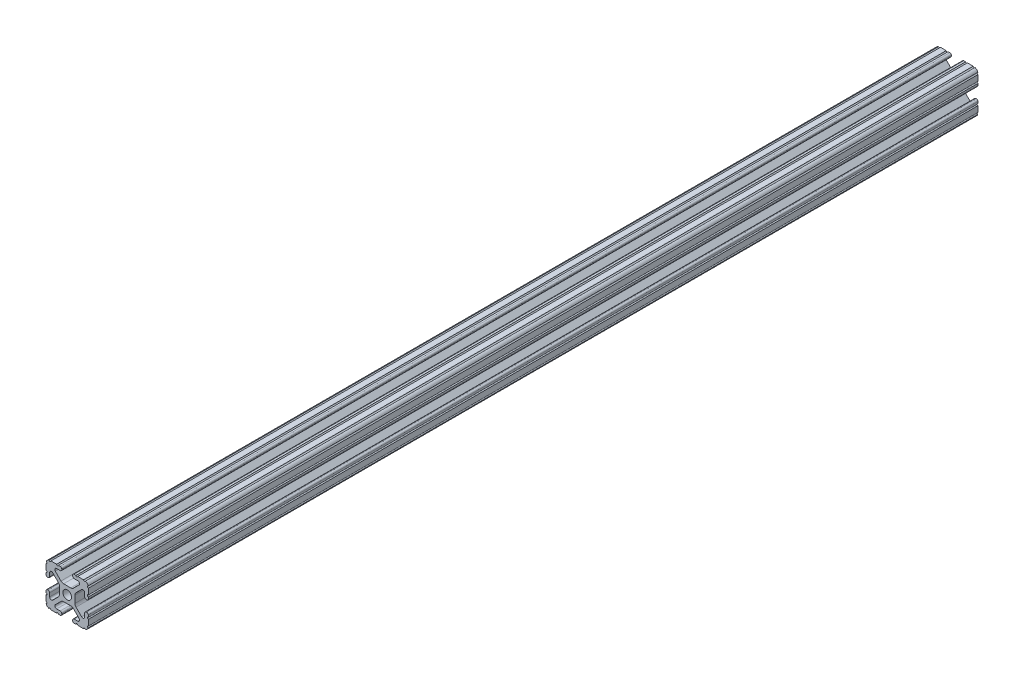
SolidWorks part; units mm, degrees
ref_plane "Front Plane" through (0, 0, 0) normal (0, 0, 1) x (1, 0, 0)
ref_plane "Top Plane" through (0, 0, 0) normal (0, 1, 0) x (1, 0, 0)
ref_plane "Right Plane" through (0, 0, 0) normal (1, 0, 0) x (0, 0, -1)
sketch "Sketch2" plane through (0, 0, 0) normal (0, 0, 1) x (1, 0, 0)
  line L0 (0, 12.7) -> (0, -12.7) construction
  line L1 (-12.7, 0) -> (12.7, 0) construction
  line L2 (3.2512, -12.7) -> (12.7, -12.7)
  line L3 (12.7, -12.7) -> (12.7, -3.2512)
  line L4 (3.2512, -12.7) -> (3.2512, -10.4902)
  line L5 (3.2512, -10.4902) -> (8.9276, -10.4902)
  line L6 (8.9276, -10.4902) -> (3.0856, -4.6482)
  line L7 (0, 0) -> (12.7, -12.7) construction
  line L8 (12.7, -3.2512) -> (10.4902, -3.2512)
  line L9 (10.4902, -3.2512) -> (10.4902, -8.9276)
  line L10 (10.4902, -8.9276) -> (4.6482, -3.0856)
  circle A0 centre (0, 0) radius 2.6035
  arc A1 (6.3485, -10.4902) -> (7.1039, -8.6665) centre (6.3485, -9.4219) ccw construction
  point P8 (0, -4.6482)
  dimension "Center Hole Diameter" = 5.207
  dimension "Rail Height" = 25.4
  dimension "Rail Width" = 25.4
  dimension "T-Slot Width" = 6.5024
  dimension "Slot Inner Width" = 14.8336
  dimension "Thickness" = 2.2098
  dimension "Slot Depth" = 5.842
  dimension "D1" = 2.2098
sketch "Sketch3" plane through (0, 0, 0) normal (1, 0, 0) x (0, 0, -1)
  line L0 (-228.6, -12.7) -> (228.6, -12.7) construction
  line L1 (-205.74, 0) -> (205.74, 0) construction
  dimension "Length" = 457.2
  dimension "D1" = 411.48
sketch "Sketch4" plane through (0, 0, 0) normal (0, 0, 1) x (1, 0, 0)
  line L0 (4.1904, -12.7) -> (10.1173, -12.7)
  line L1 (3.2512, -12.7) -> (12.7, -12.7) construction
  line L2 (3.2512, -12.7) -> (3.2512, -10.4902) construction
  line L3 (3.2512, -10.4902) -> (8.9276, -10.4902) construction
  line L4 (3.2512, -11.4294) -> (3.2512, -11.7608)
  line L5 (4.1904, -10.4902) -> (6.3485, -10.4902)
  line L6 (0, -4.6482) -> (2.164, -4.6482)
  line L7 (8.9276, -10.4902) -> (3.0856, -4.6482) construction
  line L8 (3.7373, -5.2999) -> (7.1039, -8.6665)
  line L9 (12.7, -12.7) -> (12.7, -3.2512) construction
  line L10 (10.4902, -8.9276) -> (4.6482, -3.0856) construction
  line L11 (10.4902, -3.2512) -> (10.4902, -8.9276) construction
  line L12 (10.4902, -6.3485) -> (10.4902, -4.1904)
  line L13 (12.7, -3.2512) -> (10.4902, -3.2512) construction
  line L14 (11.4294, -3.2512) -> (11.7608, -3.2512)
  line L15 (12.7, -4.1904) -> (12.7, -10.1173)
  line L16 (8.6665, -7.1039) -> (5.2999, -3.7373)
  line L17 (4.6482, 0) -> (4.6482, -2.164)
  line L18 (-12.7, 0) -> (12.7, 0) construction
  line L19 (0, -4.6482) -> (0, -2.6035)
  line L20 (0, 12.7) -> (0, -12.7) construction
  line L21 (4.6482, 0) -> (2.6035, 0)
  arc A0 (3.2512, -11.7608) -> (4.1904, -12.7) centre (4.1904, -11.7608) ccw
  arc A2 (3.2512, -11.4294) -> (4.1904, -10.4902) centre (4.1904, -11.4294) cw
  arc A3 (6.3485, -10.4902) -> (7.1039, -8.6665) centre (6.3485, -9.4219) ccw
  arc A4 (2.164, -4.6482) -> (3.7373, -5.2999) centre (2.164, -6.8732) cw
  arc A5 (10.1173, -12.7) -> (12.7, -10.1173) centre (10.1173, -10.1173) ccw
  arc A6 (8.6665, -7.1039) -> (10.4902, -6.3485) centre (9.4219, -6.3485) ccw
  arc A7 (10.4902, -4.1904) -> (11.4294, -3.2512) centre (11.4294, -4.1904) cw
  arc A8 (11.7608, -3.2512) -> (12.7, -4.1904) centre (11.7608, -4.1904) cw
  arc A9 (5.2999, -3.7373) -> (4.6482, -2.164) centre (6.8732, -2.164) cw
  circle A10 centre (0, 0) radius 2.6035 construction
  arc A11 (0, -2.6035) -> (2.6035, 0) centre (0, 0) ccw
  dimension "D1" = 2.5827
  dimension "D2" = 2.225
  dimension "D3" = 0.9392
extrude "Boss-Extrude1" add sketch "Sketch4" along normal mid plane 533.2
sketch "Sketch5" plane through (0, 0, 0) normal (0, 0, 1) x (1, 0, 0)
  line L0 (3.2512, -12.7) -> (12.7, -12.7) construction
  line L1 (4.1904, -10.4902) -> (6.3485, -10.4902) construction
  line L3 (0, 0) -> (12.7, -12.7) construction
  line L4 (6.3485, -10.4902) -> (6.3485, -12.7) construction
  line L5 (8.9276, -10.4902) -> (3.0856, -4.6482) construction
  circle A0 centre (10.3562, -12.7) radius 0.5524
  circle A1 centre (5.796, -12.7) radius 0.5524
  circle A2 centre (12.7, -10.3562) radius 0.5524
  circle A3 centre (12.7, -5.796) radius 0.5524
  point P10 (5.2694, -10.4902)
  point P12 (9.4219, -6.3485)
  dimension "D1" = 1.1049
extrude "Cut-Extrude1" cut sketch "Sketch5" against normal through all both and the other way through all
mirror "Mirror1" about plane through (0, 0, 0) normal (1, 0, 0) of bodies 137 134
mirror "Mirror2" about plane through (0, 0, 0) normal (0, 1, 0) of bodies 135
equation "\"D1@Boss-Extrude1\"=\"Length@Sketch3\""
equation "\"D1@Sketch2\"=\"Thickness@Sketch2\""
equation "\"D2@Sketch4\"=\"Slot Inner Width@Sketch2\"*0.15"
equation "\"D1@Sketch4\"=\"D3@Sketch4\"*2.75"
equation "\"D3@Sketch4\"=\"Thickness@Sketch2\"*0.425"
equation "\"D1@Sketch5\"=\"Thickness@Sketch2\"*0.5"
equation "\"D1@Sketch3\"=\"Length@Sketch3\"*0.9"
